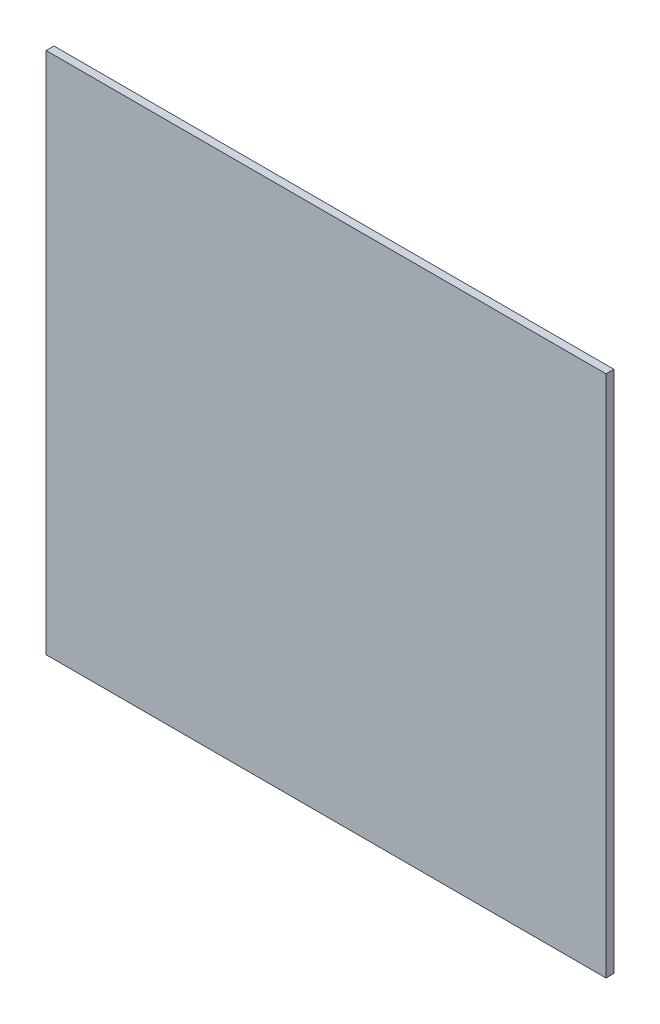
SolidWorks part; units mm, degrees
material "Glass"
ref_plane "Front Plane" through (0, 0, 0) normal (0, 0, 1) x (1, 0, 0)
ref_plane "Top Plane" through (0, 0, 0) normal (0, 1, 0) x (1, 0, 0)
ref_plane "Right Plane" through (0, 0, 0) normal (1, 0, 0) x (0, 0, -1)
sketch "Sketch1" plane through (0, 0, 0) normal (0, 0, 1) x (1, 0, 0)
  line L1 (-107, 100) -> (107, 100)
  line L2 (-107, 100) -> (-107, -100)
  line L3 (-107, -100) -> (107, -100)
  line L4 (107, 100) -> (107, -100)
  line L5 (-107, 100) -> (107, -100) construction
  line L6 (-107, -100) -> (107, 100) construction
  point P0 (0, 0)
  dimension "D1" = 214
  dimension "D2" = 200
extrude "Boss-Extrude1" add sketch "Sketch1" along normal blind 3
